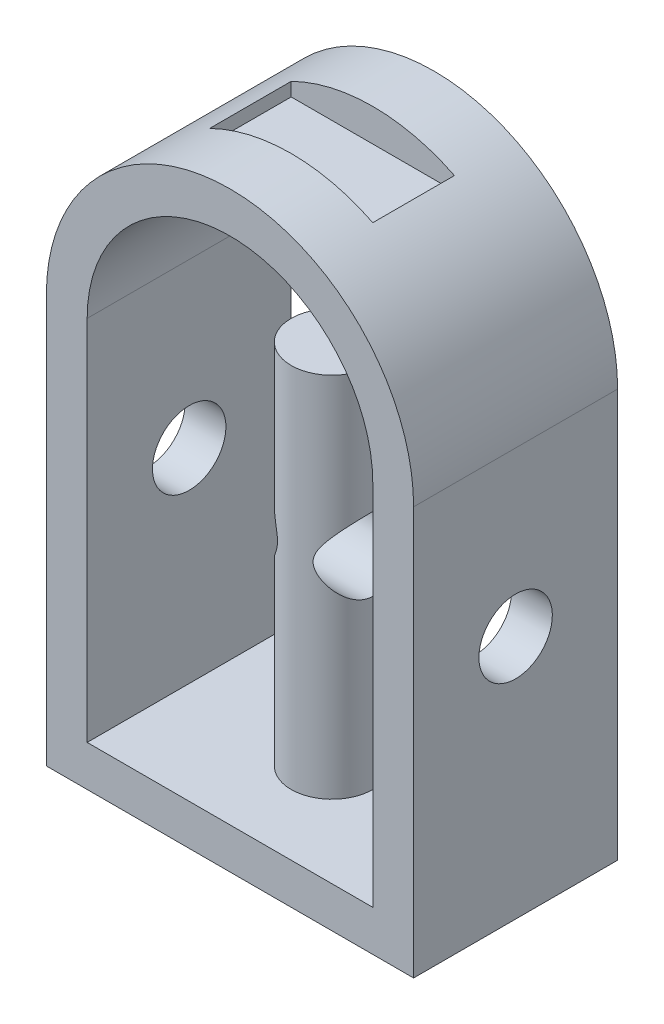
SolidWorks part; units mm, degrees
ref_plane "Front Plane" through (0, 0, 0) normal (0, 0, 1) x (1, 0, 0)
ref_plane "Top Plane" through (0, 0, 0) normal (0, 1, 0) x (1, 0, 0)
ref_plane "Right Plane" through (0, 0, 0) normal (1, 0, 0) x (0, 0, -1)
sketch "Sketch1" plane through (0, 0, 0) normal (0, 0, 1) x (1, 0, 0)
  line L0 (80, 90) -> (80, -10)
  line L2 (0, 90) -> (0, 0)
  line L3 (0, 0) -> (70, 0)
  line L4 (70, 90) -> (70, 0)
  line L5 (0, 90) -> (70, 0) construction
  line L6 (0, 0) -> (70, 90) construction
  line L7 (-10, -10) -> (80, -10)
  line L8 (-10, 90) -> (-10, -10)
  arc A0 (0, 90) -> (70, 90) centre (35, 90) cw
  arc A1 (-10, 90) -> (80, 90) centre (35, 90) cw
  dimension "D3" = 35
  dimension "D1" = 70
  dimension "D2" = 90
  dimension "D4" = 10
extrude "Boss-Extrude1" add sketch "Sketch1" along normal blind 50
ref_plane "Plane2" through (0, 135, 0) normal (0, 1, 0) x (1, 0, 0)
sketch "Sketch3" plane through (0, 135, 0) normal (0, 1, 0) x (1, 0, 0)
  line L0 (-10, -50) -> (-10, 0) construction
  line L1 (15, -15) -> (55, -15)
  line L2 (15, -15) -> (15, -35)
  line L3 (15, -35) -> (55, -35)
  line L4 (55, -15) -> (55, -35)
  line L5 (15, -15) -> (55, -35) construction
  line L6 (15, -35) -> (55, -15) construction
  line L7 (-10, -25) -> (80, -25) construction
  line L8 (80, -50) -> (80, 0) construction
  point P4 (35, -25)
  dimension "D1" = 20
  dimension "D2" = 40
extrude "Cut-Extrude1" cut sketch "Sketch3" against normal blind 8
ref_plane "Plane3" through (0, 90, 0) normal (0, 1, 0) x (1, 0, 0)
sketch "Sketch4" plane through (0, 90, 0) normal (0, 1, 0) x (1, 0, 0)
  line L0 (0, -25) -> (35, -25) construction
  line L1 (0, -50) -> (0, 0) construction
  line L2 (70, 0) -> (0, 0) construction
  line L3 (35, -25) -> (35, 0) construction
  circle A0 centre (35, -25) radius 10
  point P9 (0, -25)
  dimension "D1" = 20
extrude "Boss-Extrude2" add sketch "Sketch4" against normal up to next contours A0
ref_plane "Plane4" through (130, 0, 0) normal (-1, 0, 0) x (0, 0, 1)
sketch "Sketch6" plane through (130, 0, 0) normal (-1, 0, 0) x (0, 0, 1)
  line L0 (27.5, 90) -> (-27.5, 90) construction
  line L2 (0, 40) -> (50, 40) construction
  line L3 (0, 90) -> (0, -10) construction
  line L4 (50, 90) -> (50, -10) construction
  line L5 (25, 50) -> (25, 40) construction
  circle A0 centre (25, 50) radius 9
  dimension "D1" = 18
  dimension "D2" = 40
extrude "Cut-Extrude2" cut sketch "Sketch6" against normal through all both and the other way through all contours A0
ref_plane "Plane5" through (0, 90, 0) normal (0, 1, 0) x (0, 0, -1)
